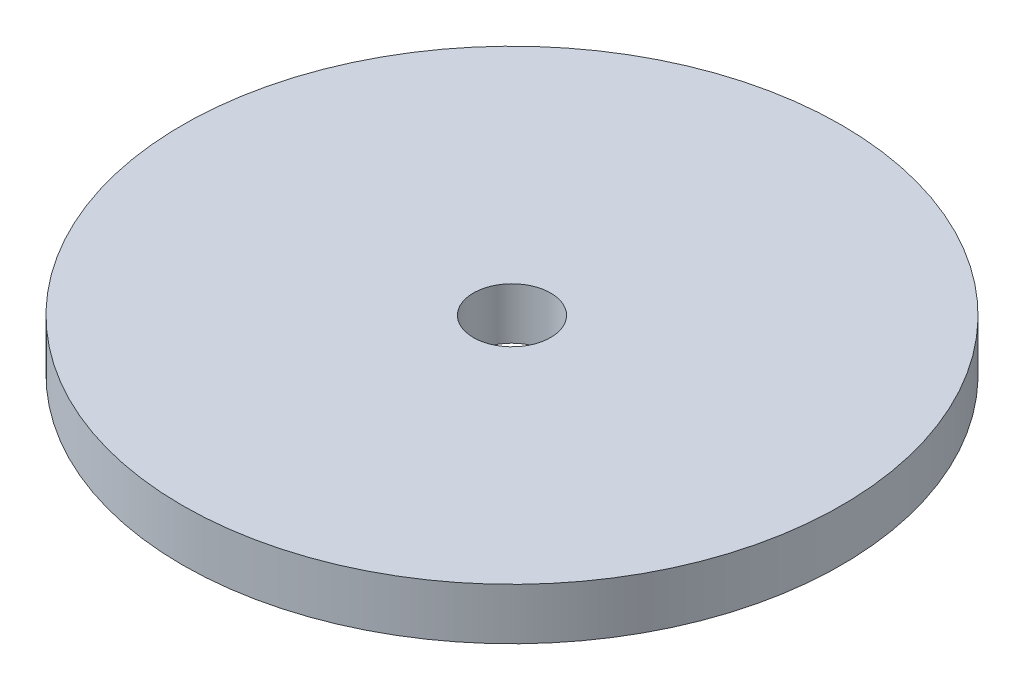
SolidWorks part; units mm, degrees
ref_plane "Front Plane" through (0, 0, 0) normal (0, 0, 1) x (1, 0, 0)
ref_plane "Top Plane" through (0, 0, 0) normal (0, 1, 0) x (1, 0, 0)
ref_plane "Right Plane" through (0, 0, 0) normal (1, 0, 0) x (0, 0, -1)
sketch "Sketch1" plane through (0, 0, 0) normal (0, 1, 0) x (1, 0, 0)
  circle A0 centre (0, 0) radius 4.7625
  circle A1 centre (0, 0) radius 40.64
  dimension "D1" = 9.525
  dimension "D2" = 81.28
extrude "Boss-Extrude1" add sketch "Sketch1" along normal blind 6.35
